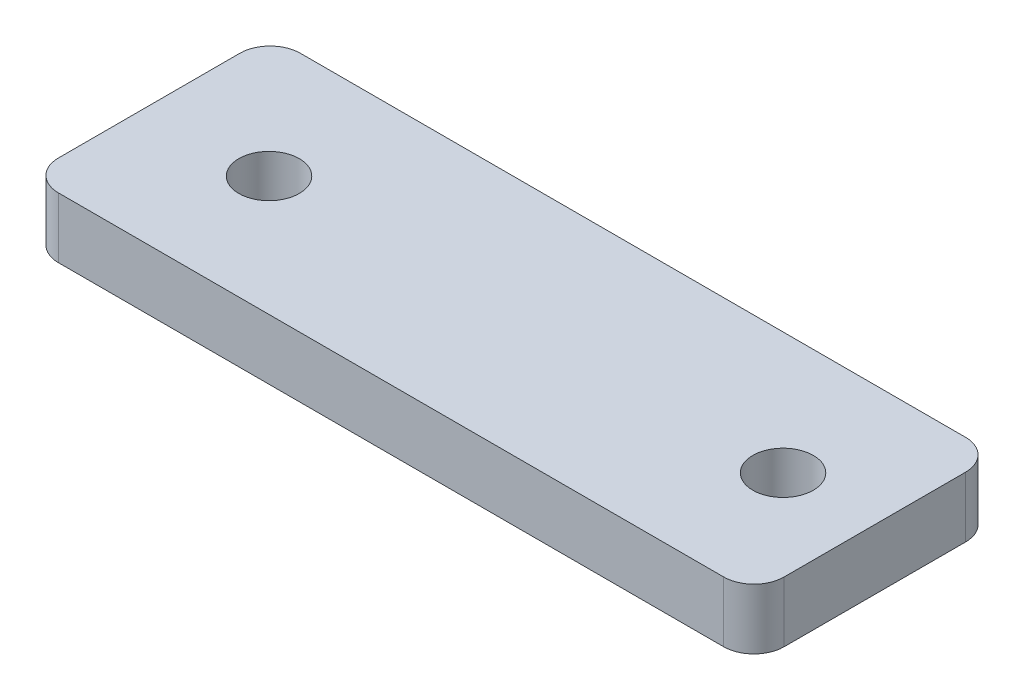
SolidWorks part; units mm, degrees
ref_plane "Front Plane" through (0, 0, 0) normal (0, 0, 1) x (1, 0, 0)
ref_plane "Top Plane" through (0, 0, 0) normal (0, 1, 0) x (1, 0, 0)
ref_plane "Right Plane" through (0, 0, 0) normal (1, 0, 0) x (0, 0, -1)
sketch "Sketch1" plane through (0, 0, 0) normal (0, 1, 0) x (1, 0, 0)
  line L1 (-40.872, 15.4756) -> (69.128, 15.4756)
  line L2 (-45.872, 10.4756) -> (-45.872, -19.5244)
  line L3 (-40.872, -24.5244) -> (69.128, -24.5244)
  line L4 (74.128, 10.4756) -> (74.128, -19.5244)
  arc A0 (74.128, 10.4756) -> (69.128, 15.4756) centre (69.128, 10.4756) ccw
  arc A1 (74.128, -19.5244) -> (69.128, -24.5244) centre (69.128, -19.5244) cw
  arc A2 (-40.872, -24.5244) -> (-45.872, -19.5244) centre (-40.872, -19.5244) cw
  arc A3 (-40.872, 15.4756) -> (-45.872, 10.4756) centre (-40.872, 10.4756) ccw
  circle A4 centre (-25.872, -4.7016) radius 5
  circle A5 centre (59.128, -4.7016) radius 5
  point P16 (-45.872, -4.5244)
  dimension "D1" = 5
  dimension "D4" = 85
  dimension "D2" = 110
  dimension "D3" = 30
  dimension "D5" = 20
extrude "Boss-Extrude1" add sketch "Sketch1" along normal blind 10
